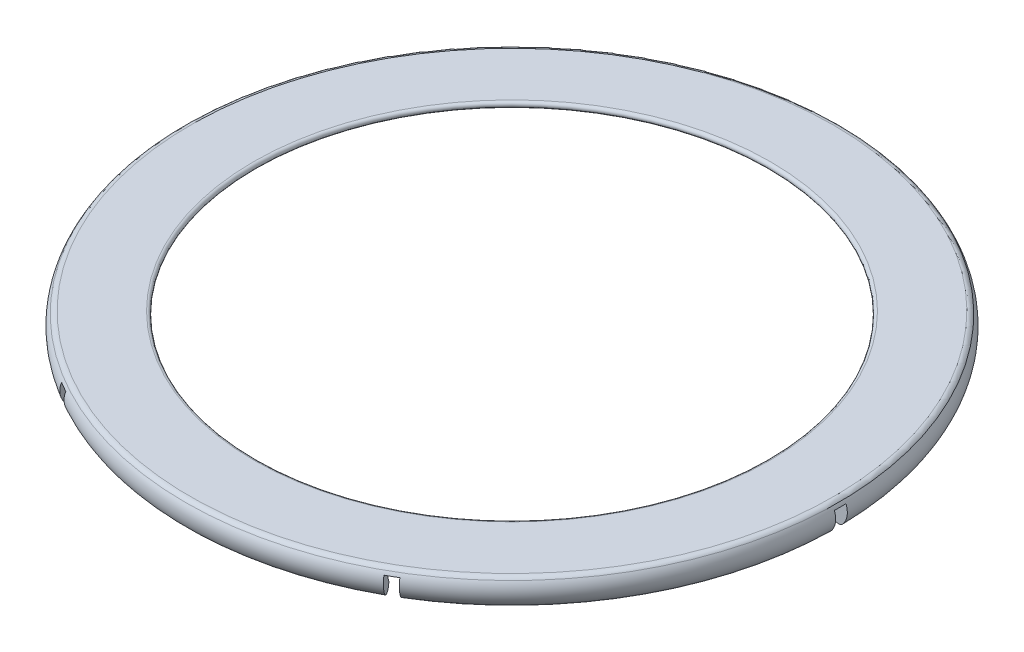
SolidWorks part; units mm, degrees
ref_plane "Front Plane" through (0, 0, 0) normal (0, 0, 1) x (1, 0, 0)
ref_plane "Top Plane" through (0, 0, 0) normal (0, 1, 0) x (1, 0, 0)
ref_plane "Right Plane" through (0, 0, 0) normal (1, 0, 0) x (0, 0, -1)
sketch "Sketch1" plane through (0, 0, 0) normal (0, 0, 1) x (1, 0, 0)
  line L0 (-26.6647, 4.6) -> (-27.8266, 4.6)
  line L1 (26.6647, 4) -> (-26.6647, 4) construction
  line L2 (-22.1647, 4.6) -> (-26.6647, 4.6)
  line L3 (-22.1647, 4) -> (-26.6647, 4) construction
  line L4 (-22.1647, 4.1) -> (-26.6647, 4.1)
  line L5 (-27.0477, 3.1786) -> (-27.1243, 3.1143) construction
  line L6 (-22.1647, 4) -> (-22.1647, 5.2432) construction
  line L7 (26.6647, 4) -> (-26.6647, 4) construction
  line L8 (26.6647, 4.1) -> (-26.6647, 4.1) construction
  line L9 (0, 0) -> (0, 13.9177) construction
  arc A0 (-26.6647, 4) -> (-26.7731, 3.0119) centre (-26.6647, 3.5) ccw construction
  arc A1 (-26.6647, 4) -> (-27.0477, 3.1786) centre (-26.6647, 3.5) ccw construction
  arc A2 (-26.6647, 4.1) -> (-27.1243, 3.1143) centre (-26.6647, 3.5) ccw
  arc A3 (-26.6647, 4) -> (-26.7731, 3.0119) centre (-26.6647, 3.5) ccw construction
  arc A4 (-26.6647, 4.1) -> (-26.7948, 2.9143) centre (-26.6647, 3.5) ccw construction
  arc A5 (-26.6647, 4.6) -> (-27.5073, 2.7929) centre (-26.6647, 3.5) ccw construction
  arc A6 (-22.1647, 4.1) -> (-22.1647, 4.6) centre (-22.1647, 4.35) ccw
  arc A7 (-27.1243, 3.1143) -> (-27.5073, 2.7929) centre (-27.3158, 2.9536) cw construction
  arc A8 (-27.8266, 4.6) -> (-27.8903, 2.4715) centre (-26.6647, 3.5) ccw
  arc A9 (-27.1243, 3.1143) -> (-27.8903, 2.4715) centre (-27.5073, 2.7929) cw
  point P25 (-27.6767, 4.6)
  dimension "D4" = 4.5
  dimension "D5" = 1
  dimension "D2" = 40
  dimension "D1" = 0.1
  dimension "D3" = 0.5
revolve "Revolve1" add sketch "Sketch1" angle 360 about L9
sketch "Sketch2" plane through (0, 4.1, 0) normal (0, -1, 0) x (1, 0, 0)
  line L1 (-38.3812, 0.5) -> (38.3812, 0.5)
  line L2 (-38.3812, 0.5) -> (-38.3812, -0.5)
  line L3 (-38.3812, -0.5) -> (38.3812, -0.5)
  line L4 (38.3812, 0.5) -> (38.3812, -0.5)
  line L5 (-38.3812, 0.5) -> (38.3812, -0.5) construction
  line L6 (-38.3812, -0.5) -> (38.3812, 0.5) construction
  point P0 (0, 0)
  point P6 (0, 0.4273)
  point P7 (0, 0)
  dimension "D1" = 1
extrude "Cut-Extrude1" cut sketch "Sketch2" along normal blind 11.684
pattern_circular "CirPattern1" count 3 over 360 about axis through (0, 0, 0) along (0, 1, 0) of "Cut-Extrude1"
fillet "Fillet1" radius 0.5 1 edges at (0, 4.6, -27.8266)
